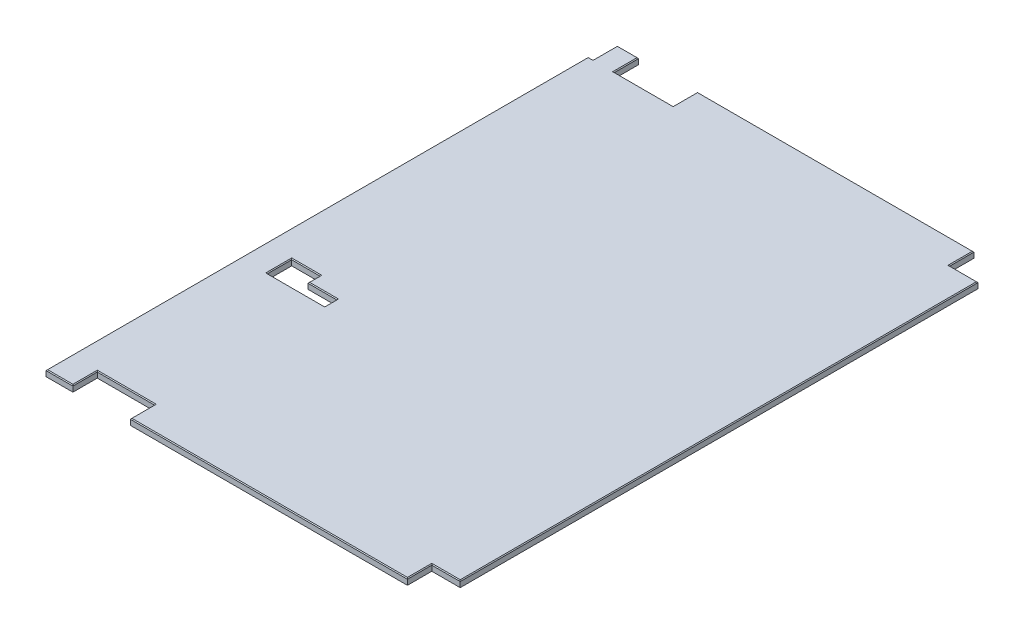
SolidWorks part; units mm, degrees
material "Oak"
ref_plane "Front Plane" through (0, 0, 0) normal (0, 0, 1) x (1, 0, 0)
ref_plane "Top Plane" through (0, 0, 0) normal (0, 1, 0) x (1, 0, 0)
ref_plane "Right Plane" through (0, 0, 0) normal (1, 0, 0) x (0, 0, -1)
sketch "Sketch1" plane through (0, 0, 0) normal (0, 1, 0) x (1, 0, 0)
  line L1 (0, 1771.65) -> (1219.2, 1771.65)
  line L2 (0, 1771.65) -> (0, 0)
  line L3 (0, 0) -> (1219.2, 0)
  line L4 (1219.2, 1771.65) -> (1219.2, 0)
  dimension "D1" = 1771.65
  dimension "D2" = 1219.2
extrude "Boss-Extrude1" add sketch "Sketch1" along normal mid plane 19.05
sketch "Sketch3" plane through (0, 9.525, 0) normal (0, 1, 0) x (1, 0, 0)
  line L12 (81.7118, 1771.65) -> (265.8491, 1771.65)
  line L13 (81.7118, 1771.65) -> (81.7118, 1695.45)
  line L14 (81.7118, 1695.45) -> (265.8491, 1695.45)
  line L15 (265.8491, 1771.65) -> (265.8491, 1695.45)
  line L16 (1130.3, 1771.65) -> (1219.2, 1771.65)
  line L17 (1130.3, 1771.65) -> (1130.3, 1695.45)
  line L18 (1130.3, 1695.45) -> (1219.2, 1695.45)
  line L19 (1219.2, 1771.65) -> (1219.2, 1695.45)
  line L24 (84.1756, 684.2125) -> (173.1672, 684.2125)
  line L25 (84.1756, 684.2125) -> (84.1756, 608.0125)
  line L26 (84.1756, 608.0125) -> (263.5631, 608.0125)
  line L27 (263.5631, 646.1252) -> (263.5631, 608.0125)
  line L28 (173.1672, 684.2125) -> (173.1672, 646.1252)
  line L29 (173.1672, 646.1252) -> (263.5631, 646.1252)
  line L38 (263.5631, 0) -> (84.1756, 0)
  line L39 (263.5631, 0) -> (263.5631, 76.2)
  line L40 (263.5631, 76.2) -> (84.1756, 76.2)
  line L41 (84.1756, 0) -> (84.1756, 76.2)
  line L42 (1219.2, 0) -> (1130.3, 0)
  line L43 (1219.2, 0) -> (1219.2, 76.2)
  line L44 (1219.2, 76.2) -> (1130.3, 76.2)
  line L45 (1130.3, 0) -> (1130.3, 76.2)
  line L50 (1219.2, 0) -> (1219.2, 1771.65) construction
  line L52 (1219.2, 0) -> (1219.2, 1771.65) construction
  line L55 (0, 1771.65) -> (15.2273, 1771.65)
  line L57 (0, 1695.45) -> (15.2273, 1695.45)
  line L58 (15.2273, 1771.65) -> (15.2273, 1695.45)
  line L59 (0, 0) -> (1219.2, 0) construction
  line L61 (0, 1771.65) -> (0, 1695.45)
  dimension "D2" = 15.2273
  dimension "D3" = 179.3875
  dimension "D4" = 81.7118
  dimension "D5" = 88.9
  dimension "D6" = 1130.3
  dimension "D7" = 179.3875
  dimension "D8" = 88.9916
  dimension "D9" = 84.1756
  dimension "D10" = 1130.3
  dimension "D11" = 184.1373
  dimension "D13" = 88.9
  dimension "D14" = 76.2
  dimension "D15" = 608.0125
  dimension "D16" = 76.2
  dimension "D17" = 38.1127
  dimension "D18" = 1695.45
  dimension "D19" = 84.1756
other "AlignGroup3"
other "AlignGroup4"
extrude "Cut-Extrude2" cut sketch "Sketch3" against normal through all
chamfer "Chamfer1" distance 2.54 angle 45 24 edges at (173.8694, 9.525, -608.0125) (263.5631, 9.525, -627.0688) (218.3651, 9.525, -646.1252) (173.1672, 9.525, -665.1688) (128.6714, 9.525, -684.2125) (84.1756, 9.525, -646.1125) (48.4695, 9.525, -1771.65) (81.7118, 9.525, -1733.55) (173.7805, 9.525, -1695.45) (265.8491, 9.525, -1733.55) (698.0746, 9.525, -1771.65) (1130.3, 9.525, -1733.55) (1174.75, 9.525, -1695.45) (1219.2, 9.525, -885.825) (1174.75, 9.525, -76.2) (1130.3, 9.525, -38.1) (696.9315, 9.525, 0) (263.5631, 9.525, -38.1) (173.8693, 9.525, -76.2) (84.1756, 9.525, -38.1) (42.0878, 9.525, 0) (0, 9.525, -847.725) (7.6136, 9.525, -1695.45) (15.2273, 9.525, -1733.55)
